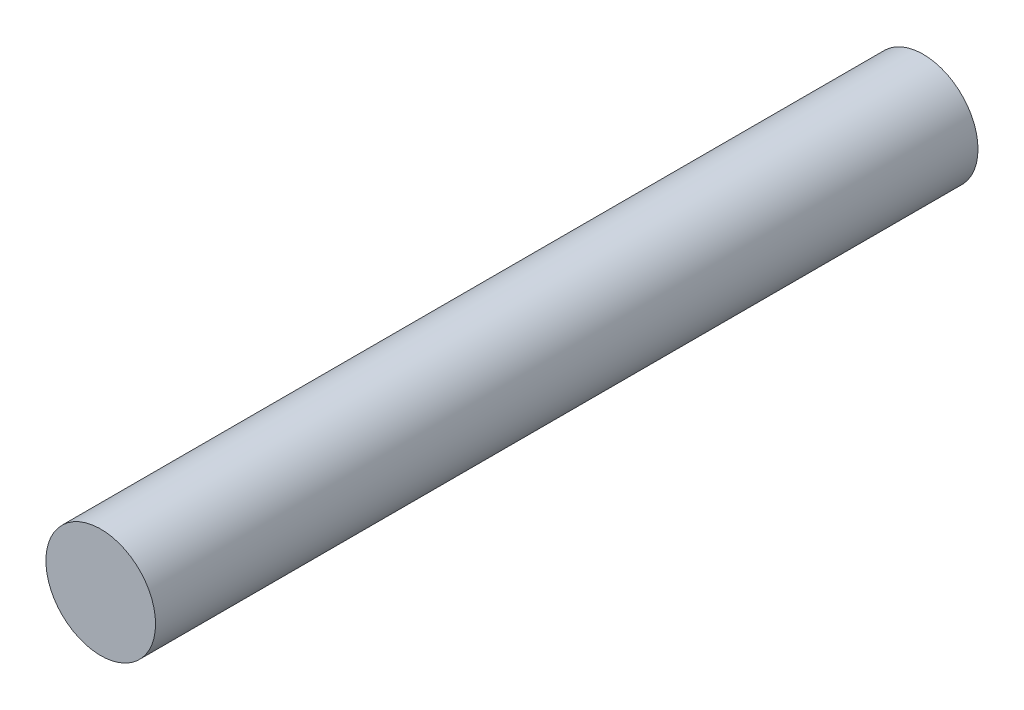
SolidWorks part; units mm, degrees
ref_plane "Front Plane" through (0, 0, 0) normal (0, 0, 1) x (1, 0, 0)
ref_plane "Top Plane" through (0, 0, 0) normal (0, 1, 0) x (1, 0, 0)
ref_plane "Right Plane" through (0, 0, 0) normal (1, 0, 0) x (0, 0, -1)
sketch "Sketch1" plane through (0, 0, 0) normal (0, 0, 1) x (1, 0, 0)
  circle A0 centre (0, 0) radius 10
  dimension "D1" = 20
extrude "Boss-Extrude1" add sketch "Sketch1" along normal blind 150
sketch "Sketch2" plane through (0, 0, 0) normal (0, 0, -1) x (-1, 0, 0)
  circle A0 centre (0, 0) radius 5
  dimension "D1" = 10
extrude "Cut-Extrude1" cut sketch "Sketch2" against normal blind 123
